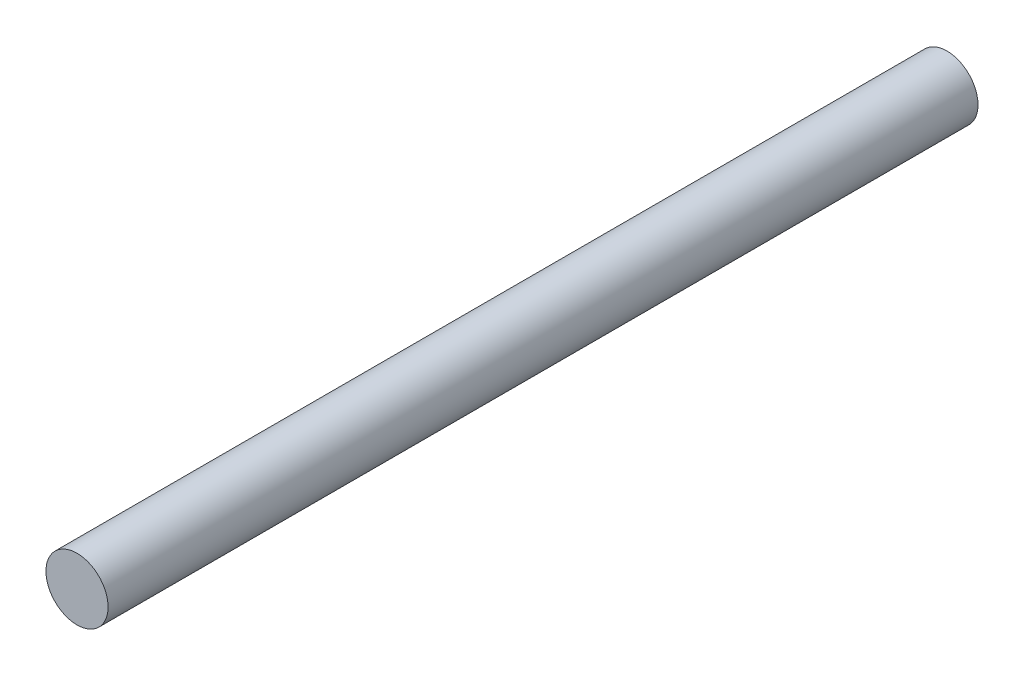
SolidWorks part; units mm, degrees
ref_plane "Front Plane" through (0, 0, 0) normal (0, 0, 1) x (1, 0, 0)
ref_plane "Top Plane" through (0, 0, 0) normal (0, 1, 0) x (1, 0, 0)
ref_plane "Right Plane" through (0, 0, 0) normal (1, 0, 0) x (0, 0, -1)
sketch "Sketch1" plane through (0, 0, 0) normal (0, 0, 1) x (1, 0, 0)
  circle A0 centre (0, 0) radius 5
  dimension "D1" = 10
extrude "Boss-Extrude1" add sketch "Sketch1" along normal mid plane 140
ref_plane "Plane1" through (0, 0, -25.74) normal (0, 0, 1) x (1, 0, 0)
ref_plane "Plane2" through (0, 0, -15.74) normal (0, 0, 1) x (1, 0, 0)
sketch "Sketch3" plane through (0, 0, 70) normal (0, 0, 1) x (1, 0, 0)
  circle A0 centre (0, 0) radius 5
sketch "Sketch4" plane through (0, 0, -70) normal (0, 0, -1) x (-1, 0, 0)
  circle A0 centre (0, 0) radius 5
